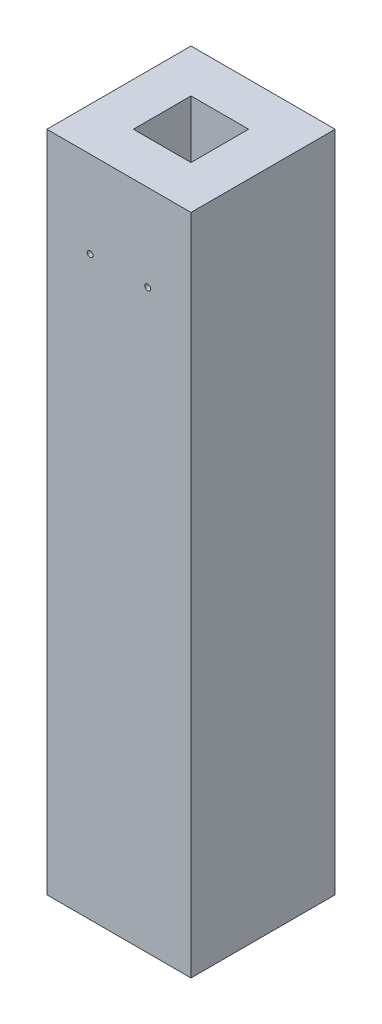
SolidWorks part; units mm, degrees
ref_plane "Front Plane" through (0, 0, 0) normal (0, 0, 1) x (1, 0, 0)
ref_plane "Top Plane" through (0, 0, 0) normal (0, 1, 0) x (1, 0, 0)
ref_plane "Right Plane" through (0, 0, 0) normal (1, 0, 0) x (0, 0, -1)
sketch "Sketch1" plane through (0, 0, 0) normal (0, 1, 0) x (1, 0, 0)
  line L1 (25, 25) -> (-25, 25)
  line L2 (25, 25) -> (25, -25)
  line L3 (25, -25) -> (-25, -25)
  line L4 (-25, 25) -> (-25, -25)
  line L5 (25, 25) -> (-25, -25) construction
  line L6 (25, -25) -> (-25, 25) construction
  point P0 (0, 0)
  dimension "D1" = 50
  dimension "D2" = 50
extrude "Boss-Extrude1" add sketch "Sketch1" along normal blind 230
sketch "Sketch2" plane through (0, 0, 0) normal (0, -1, 0) x (-1, 0, 0)
  line L1 (-15, -12.5) -> (15, -12.5)
  line L2 (-15, -12.5) -> (-15, 12.5)
  line L3 (-15, 12.5) -> (15, 12.5)
  line L4 (15, -12.5) -> (15, 12.5)
  line L5 (-15, -12.5) -> (15, 12.5) construction
  line L6 (-15, 12.5) -> (15, -12.5) construction
  point P0 (0, 0)
  dimension "D1" = 25
  dimension "D2" = 30
extrude "Boss-Extrude2" add sketch "Sketch2" along normal blind 10
sketch "Sketch3" plane through (0, -10, 0) normal (0, -1, 0) x (-1, 0, 0)
  circle A0 centre (0, 0) radius 5
  dimension "D1" = 10
extrude "Cut-Extrude1" cut sketch "Sketch3" against normal blind 100
sketch "Sketch4" plane through (0, 230, 0) normal (0, 1, 0) x (1, 0, 0)
  line L1 (10, 10) -> (-10, 10)
  line L2 (10, 10) -> (10, -10)
  line L3 (10, -10) -> (-10, -10)
  line L4 (-10, 10) -> (-10, -10)
  line L5 (10, 10) -> (-10, -10) construction
  line L6 (10, -10) -> (-10, 10) construction
  point P0 (0, 0)
  dimension "D1" = 20
  dimension "D2" = 20
extrude "Cut-Extrude2" cut sketch "Sketch4" against normal blind 21
sketch "Sketch5" plane through (0, 0, 25) normal (0, 0, 1) x (1, 0, 0)
  line L0 (-25, 230) -> (25, 230) construction
  line L1 (25, 230) -> (25, 0) construction
  line L2 (-25, 230) -> (-25, 0) construction
  circle A0 centre (10, 200) radius 1
  circle A1 centre (-10, 200) radius 1
  dimension "D1" = 2
  dimension "D2" = 2
  dimension "D3" = 30
  dimension "D4" = 30
  dimension "D5" = 15
  dimension "D6" = 15
extrude "Cut-Extrude3" cut sketch "Sketch5" against normal blind 15
